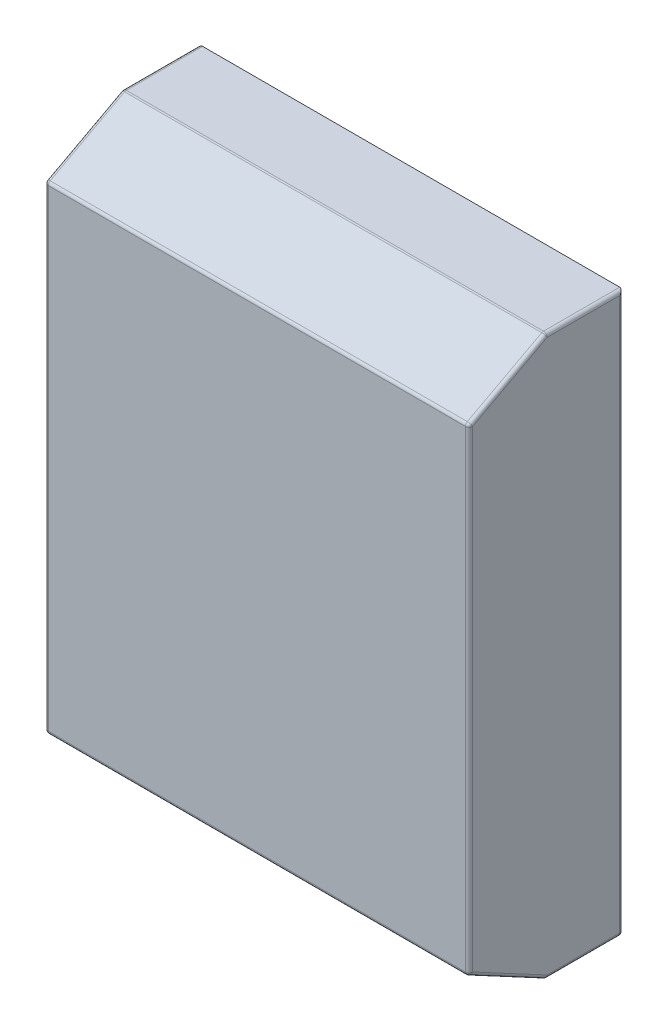
SolidWorks part; units mm, degrees
other "Camera1"
ref_plane "Back Wall Plane" through (0, 0, 0) normal (0, 0, 1) x (1, 0, 0)
ref_plane "Top Plane" through (0, 0, 0) normal (0, 1, 0) x (1, 0, 0)
ref_plane "Right Plane" through (0, 0, 0) normal (1, 0, 0) x (0, 0, -1)
sketch "Sketch1" plane through (0, 0, 0) normal (0, 0, 1) x (1, 0, 0)
  line L1 (-74.0511, 169.9391) -> (205.3489, 169.9391)
  line L2 (-74.0511, 169.9391) -> (-74.0511, -198.3609)
  line L3 (-74.0511, -198.3609) -> (205.3489, -198.3609)
  line L4 (205.3489, 169.9391) -> (205.3489, -198.3609)
  dimension "D1" = 368.3
  dimension "D2" = 279.4
extrude "Boss-Extrude1" add sketch "Sketch1" along normal blind 101.6
sketch "Sketch5" plane through (-74.0511, 0, 0) normal (-1, 0, 0) x (0, 0, 1)
  line L0 (0, -14.2109) -> (101.6, -14.2109) construction
  line L1 (0, 169.9391) -> (0, -198.3609) construction
  line L2 (101.6, 169.9391) -> (101.6, -198.3609) construction
  line L4 (50.8, 169.9391) -> (101.6, 142.7647)
  line L5 (101.6, 169.9391) -> (0, 169.9391) construction
  line L6 (101.6, 142.7647) -> (197.2713, 191.7438)
  line L7 (197.2713, 191.7438) -> (59.2215, 225.543)
  line L8 (59.2215, 225.543) -> (50.8, 169.9391)
  line L9 (197.2713, -220.1656) -> (59.2215, -253.9648)
  line L10 (101.6, -171.1866) -> (197.2713, -220.1656)
  line L11 (50.8, -198.3609) -> (101.6, -171.1866)
  line L12 (59.2215, -253.9648) -> (50.8, -198.3609)
extrude "Cut-Extrude2" cut sketch "Sketch5" against normal blind 343.662
ref_plane "Plane1" through (0, -200.9009, 0) normal (0, -1, 0) x (-1, 0, 0)
sketch "Sketch6" plane through (0, -200.9009, 0) normal (0, -1, 0) x (-1, 0, 0)
  line L0 (-65.6489, 0) -> (-65.6489, -101.6) construction
  line L1 (74.0511, 0) -> (-205.3489, 0) construction
  line L2 (-205.3489, -101.6) -> (74.0511, -101.6) construction
  line L3 (47.4659, -87.3509) -> (-178.7638, -87.3509)
  line L4 (-178.7638, -68.3009) -> (47.4659, -68.3009)
  arc A0 (47.4659, -68.3009) -> (47.4659, -87.3509) centre (47.4659, -77.8259) cw
  arc A1 (-178.7638, -68.3009) -> (-178.7638, -87.3509) centre (-178.7638, -77.8259) ccw
  point P12 (-65.6489, -68.3009)
  point P14 (-65.6489, -87.3509)
  dimension "D1" = 19.05
extrude "Cut-Extrude3" cut sketch "Sketch6" against normal blind 81.788
fillet "Fillet2" radius 2.38 17 edges at (65.6489, -198.3609, 0) (-74.0511, -198.3609, 25.4) (65.6489, -198.3609, 50.8) (205.3489, -198.3609, 25.4) (65.6489, -171.1866, 101.6) (-74.0511, -184.7738, 76.2) (205.3489, -184.7738, 76.2) (205.3489, -14.2109, 0) (-74.0511, -14.2109, 101.6) (205.3489, -14.2109, 101.6) (65.6489, 142.7647, 101.6) (205.3489, 169.9391, 25.4) (205.3489, 156.3519, 76.2) (-74.0511, 156.3519, 76.2) (-74.0511, -14.2109, 0) (65.6489, 169.9391, 50.8) (-74.0511, 169.9391, 25.4)
